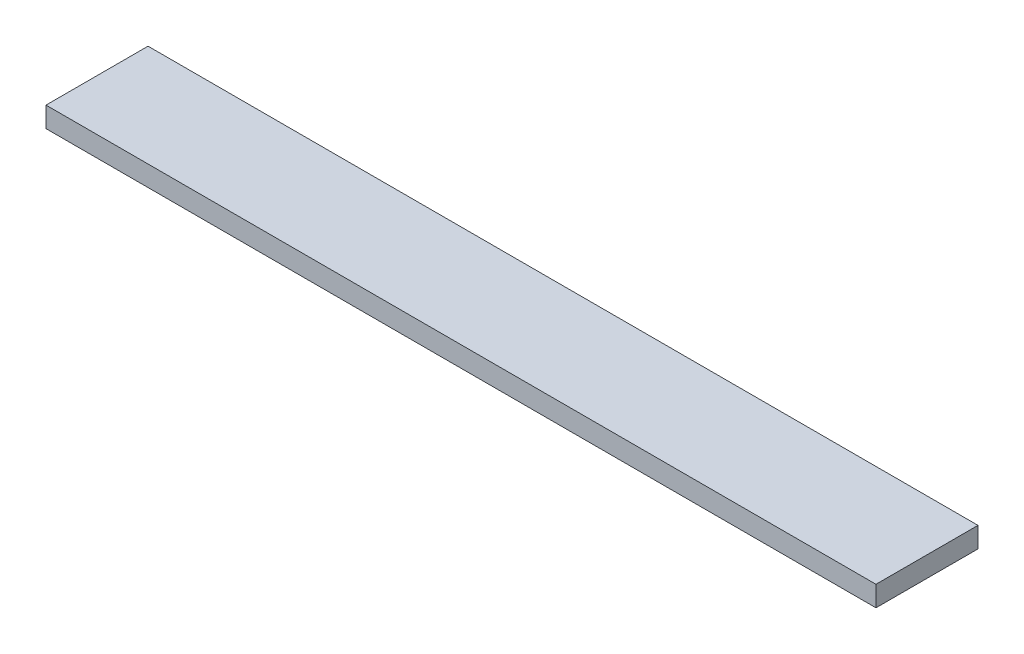
SolidWorks part; units mm, degrees
ref_plane "Front Plane" through (0, 0, 0) normal (0, 0, 1) x (1, 0, 0)
ref_plane "Top Plane" through (0, 0, 0) normal (0, 1, 0) x (1, 0, 0)
ref_plane "Right Plane" through (0, 0, 0) normal (1, 0, 0) x (0, 0, -1)
sketch "Sketch1" plane through (0, 0, 0) normal (0, 1, 0) x (1, 0, 0)
  line L1 (0, 0) -> (122, 0)
  line L2 (0, 0) -> (0, 15)
  line L3 (0, 15) -> (122, 15)
  line L4 (122, 0) -> (122, 15)
  dimension "D1" = 122
  dimension "D2" = 15
extrude "Boss-Extrude1" add sketch "Sketch1" along normal blind 3
